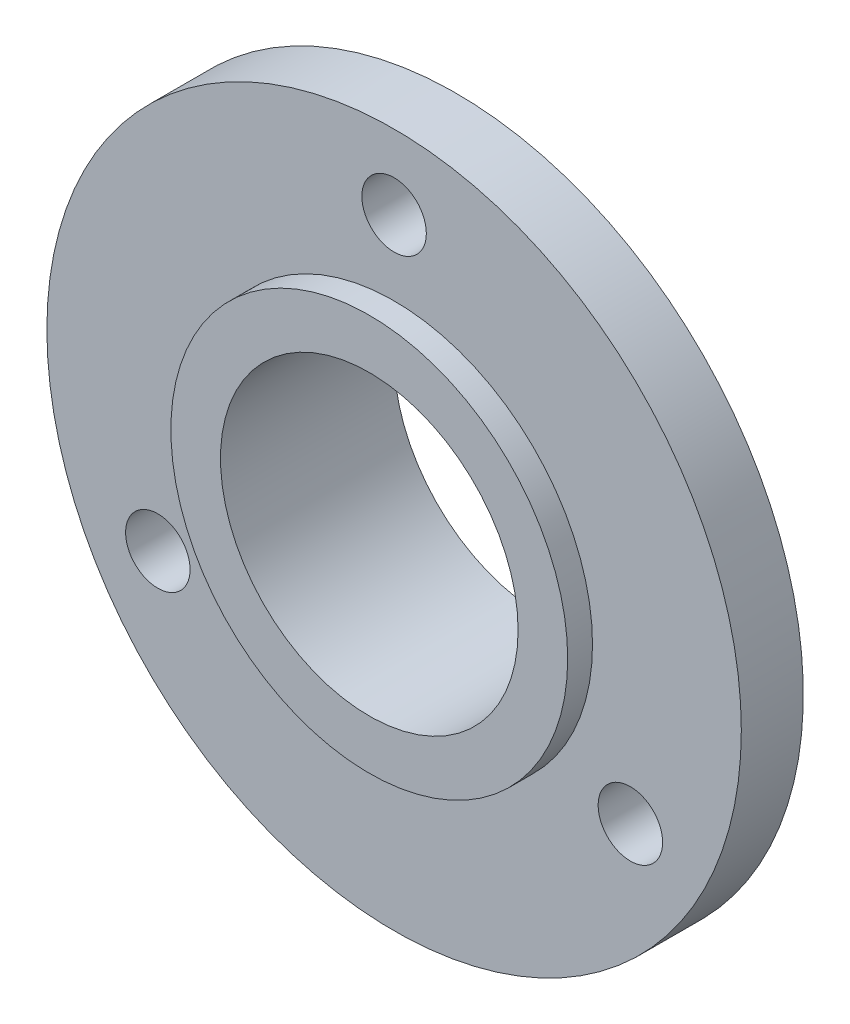
SolidWorks part; units mm, degrees
material "POM copolymère d'acétal"
ref_plane "Plan de face" through (0, 0, 0) normal (0, 0, 1) x (1, 0, 0)
ref_plane "Plan de dessus" through (0, 0, 0) normal (0, 1, 0) x (1, 0, 0)
ref_plane "Plan de droite" through (0, 0, 0) normal (1, 0, 0) x (0, 0, -1)
sketch "Esquisse1" plane through (0, 0, 0) normal (0, 0, 1) x (1, 0, 0)
  circle A0 centre (0, 0) radius 14
  circle A1 centre (0, 0) radius 6
  dimension "D1" = 28
  dimension "D2" = 12
extrude "Boss.-Extru.1" add sketch "Esquisse1" along normal blind 7
sketch "Esquisse2" plane through (0, 0, 7) normal (0, 0, 1) x (1, 0, 0)
  circle A0 centre (0, 0) radius 14
  circle A1 centre (0, 0) radius 8
  dimension "D1" = 28
  dimension "D2" = 16
extrude "Enlèv. mat.-Extru.1" cut sketch "Esquisse2" against normal blind 1
sketch "Esquisse3" plane through (0, 0, 0) normal (0, 0, -1) x (-1, 0, 0)
  circle A0 centre (0, 0) radius 8
  dimension "D1" = 16
extrude "Enlèv. mat.-Extru.2" cut sketch "Esquisse3" against normal blind 3.5 flip side to cut
sketch "Esquisse4" plane through (0, 0, 0) normal (0, 0, 1) x (1, 0, 0)
  line L0 (0, 0) -> (0, 14) construction
  circle A0 centre (0, 0) radius 14 construction
  circle A1 centre (0, 11) radius 1.3
  dimension "D1" = 2.6
  dimension "D2" = 3
extrude "Enlèv. mat.-Extru.3" cut sketch "Esquisse4" along normal blind 8
pattern_circular "Répétition circulaire1" count 3 over 360 about axis through (0, 0, 0) along (0, 0, 1) of "Enlèv. mat.-Extru.3"
